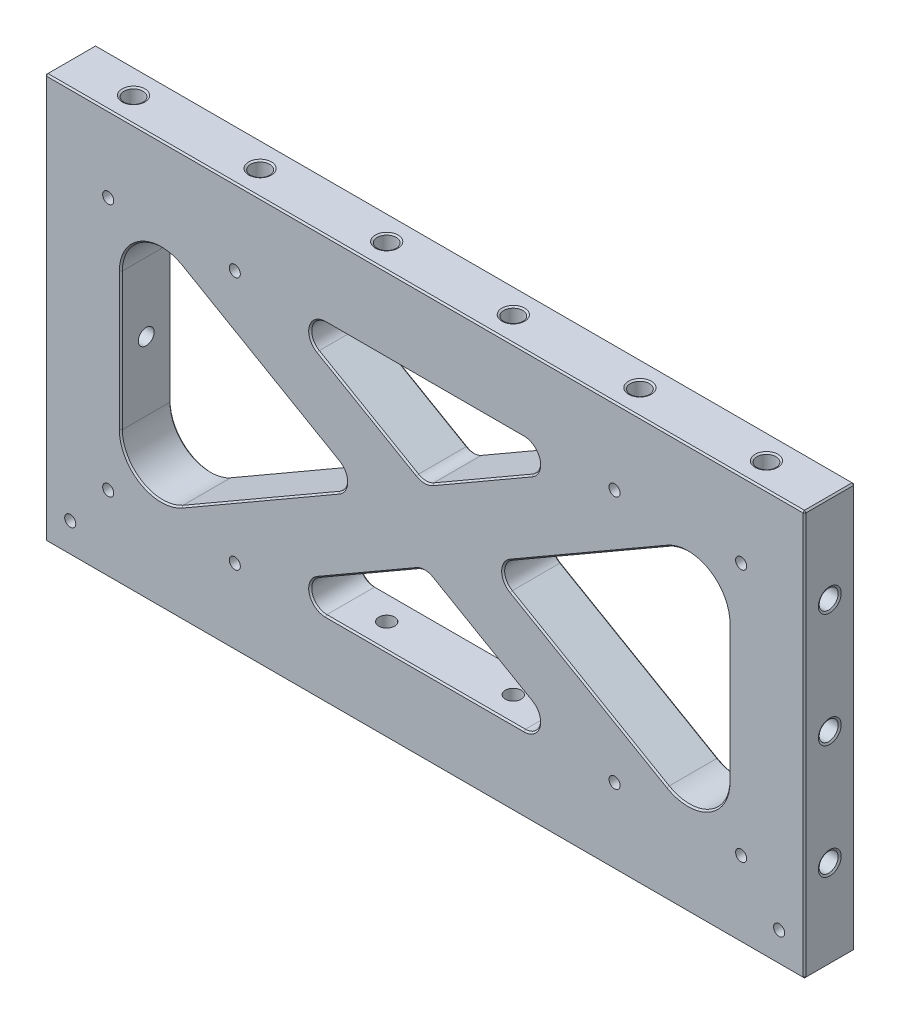
SolidWorks part; units mm, degrees
material "6061-T6 Al"
ref_plane "Front" through (0, 0, 0) normal (0, 0, 1) x (1, 0, 0)
ref_plane "Top" through (0, 0, 0) normal (0, 1, 0) x (1, 0, 0)
ref_plane "Right" through (0, 0, 0) normal (1, 0, 0) x (0, 0, -1)
sketch "Sketch1" plane through (0, 0, 0) normal (0, 0, 1) x (1, 0, 0)
  line L1 (-190.5, 0) -> (190.5, 0)
  line L2 (-190.5, 0) -> (-190.5, 203.2)
  line L3 (-190.5, 203.2) -> (190.5, 203.2)
  line L4 (190.5, 0) -> (190.5, 203.2)
  dimension "D1" = 203.2
  dimension "D2" = 381
extrude "Extrude1" add sketch "Sketch1" along normal mid plane 25.4
sketch "Sketch22" plane through (0, 0, 12.7) normal (0, 0, 1) x (1, 0, 0)
  line L0 (0, 0) -> (0, 38.1) construction
  line L1 (-152.4, 165.1) -> (152.4, 165.1)
  line L2 (-152.4, 165.1) -> (-152.4, 38.1)
  line L3 (-152.4, 38.1) -> (152.4, 38.1)
  line L4 (152.4, 165.1) -> (152.4, 38.1)
  line L5 (152.4, 101.6) -> (190.5, 101.6) construction
  line L6 (190.5, 0) -> (190.5, 203.2) construction
  line L7 (-190.5, 0) -> (190.5, 0) construction
  dimension "D1" = 38.1
  dimension "D2" = 38.1
extrude "Extrude2" cut sketch "Sketch22" against normal through all
sketch "Sketch23" plane through (0, 0, 12.7) normal (0, 0, 1) x (1, 0, 0)
  line L0 (-141.7352, 165.1) -> (78.2352, 38.1)
  line L1 (152.4, 165.1) -> (-152.4, 165.1) construction
  line L2 (-152.4, 38.1) -> (152.4, 38.1) construction
  line L3 (78.2352, 38.1) -> (141.7352, 38.1)
  line L4 (141.7352, 38.1) -> (-78.2352, 165.1)
  line L5 (-78.2352, 165.1) -> (-141.7352, 165.1)
  line L6 (-109.9852, 165.1) -> (109.9852, 38.1) construction
  point P10 (0, 101.6)
  dimension "D1" = 31.75
  dimension "D2" = 30
extrude "Extrude3" add sketch "Sketch23" against normal up to surface (25.4 mm away) up to face at (0, 101.6, -12.7)
mirror "Mirror2" about plane through (0, 0, 0) normal (1, 0, 0) of "Extrude3"
sketch "Sketch25" plane through (0, 0, -12.7) normal (0, 0, -1) x (-1, 0, 0)
  line L0 (-152.4, 136.062) -> (-152.4, 165.1)
  line L1 (-152.4, 38.1) -> (-152.4, 165.1) construction
  line L2 (-152.4, 165.1) -> (-141.7352, 165.1)
  line L3 (-141.7352, 165.1) -> (-121.92, 153.6597)
  line L4 (-141.7352, 165.1) -> (-31.75, 101.6) construction
  line L5 (0, 119.9309) -> (0, 165.1) construction
  line L6 (-78.2352, 165.1) -> (78.2352, 165.1) construction
  line L7 (141.7352, 165.1) -> (121.92, 153.6597)
  line L8 (152.4, 165.1) -> (141.7352, 165.1)
  line L9 (152.4, 136.062) -> (152.4, 165.1)
  line L10 (31.75, 101.6) -> (152.4, 101.6) construction
  line L11 (152.4, 165.1) -> (152.4, 38.1) construction
  line L12 (152.4, 67.138) -> (152.4, 38.1)
  line L13 (152.4, 38.1) -> (141.7352, 38.1)
  line L14 (141.7352, 38.1) -> (121.92, 49.5403)
  line L15 (-141.7352, 38.1) -> (-121.92, 49.5403)
  line L16 (-152.4, 38.1) -> (-141.7352, 38.1)
  line L17 (-152.4, 67.138) -> (-152.4, 38.1)
  arc A0 (-152.4, 136.062) -> (-121.92, 153.6597) centre (-132.08, 136.062) cw
  arc A1 (152.4, 136.062) -> (121.92, 153.6597) centre (132.08, 136.062) ccw
  arc A2 (152.4, 67.138) -> (121.92, 49.5403) centre (132.08, 67.138) cw
  arc A3 (-152.4, 67.138) -> (-121.92, 49.5403) centre (-132.08, 67.138) ccw
  dimension "D1" = 20.32
extrude "Extrude4" add sketch "Sketch25" against normal up to surface (25.4 mm away) up to face at (124.0041, 101.6, 12.7)
fillet "Fillet2" radius 7.62 8 edges at (-78.2352, 165.1, 0) (78.2352, 165.1, 0) (0, 119.9309, 0) (0, 83.2691, 0) (78.2352, 38.1, 0) (-78.2352, 38.1, 0) (-31.75, 101.6, 0) (31.75, 101.6, 0)
chamfer "Chamfer1" distance 0.762 angle 45 12 edges at (0, 0, 12.7) (190.5, 0, 0) (0, 0, -12.7) (-190.5, 101.6, 12.7) (-190.5, 0, 0) (-190.5, 101.6, -12.7) (190.5, 203.2, 0) (0, 203.2, 12.7) (-190.5, 203.2, 0) (0, 203.2, -12.7) (190.5, 101.6, 12.7) (190.5, 101.6, -12.7)
chamfer "Chamfer2" distance 0.762 angle 45 48 edges at (142.24, 153.6597, 12.7) (142.24, 153.6597, -12.7) (152.4, 101.6, 12.7) (82.55, 130.9294, 12.7) (82.55, 130.9294, -12.7) (142.24, 49.5403, 12.7) (142.24, 49.5403, -12.7) (39.37, 101.6, 12.7) (82.55, 72.2706, 12.7) (82.55, 72.2706, -12.7) (152.4, 101.6, -12.7) (39.37, 101.6, -12.7) (57.1574, 159.4522, 12.7) (28.7085, 136.5057, 12.7) (28.7085, 136.5057, -12.7) (0, 165.1, 12.7) (0, 121.1097, 12.7) (-57.1574, 159.4522, 12.7) (-28.7085, 136.5057, 12.7) (-28.7085, 136.5057, -12.7) (57.1574, 159.4522, -12.7) (0, 165.1, -12.7) (0, 121.1097, -12.7) (-57.1574, 159.4522, -12.7) (-82.55, 130.9294, -12.7) (-82.55, 130.9294, 12.7) (-142.24, 153.6597, 12.7) (-142.24, 153.6597, -12.7) (-39.37, 101.6, -12.7) (-152.4, 101.6, -12.7) (-82.55, 72.2706, 12.7) (-82.55, 72.2706, -12.7) (-142.24, 49.5403, 12.7) (-142.24, 49.5403, -12.7) (-39.37, 101.6, 12.7) (-152.4, 101.6, 12.7) (0, 82.0903, -12.7) (-28.7085, 66.6943, -12.7) (-28.7085, 66.6943, 12.7) (28.7085, 66.6943, 12.7) (28.7085, 66.6943, -12.7) (-57.1574, 43.7478, -12.7) (57.1574, 43.7478, -12.7) (0, 38.1, -12.7) (0, 82.0903, 12.7) (-57.1574, 43.7478, 12.7) (57.1574, 43.7478, 12.7) (0, 38.1, 12.7)
hole_wizard "3/8-16 Tapped Hole1" positions "Sketch7" profile "Sketch6" tap size "3/8-16" standard "Ansi Inch"
sketch "Sketch7" plane through (0, 0, 0) normal (0, -1, 0) x (1, 0, 0)
  line L8 (-158.75, 0) -> (-95.25, 0) construction
  line L9 (-95.25, 0) -> (-31.75, 0) construction
  line L10 (-31.75, 0) -> (31.75, 0) construction
  line L11 (31.75, 0) -> (95.25, 0) construction
  line L12 (95.25, 0) -> (158.75, 0) construction
  point P5 (-31.75, 0)
  point P7 (31.75, 0)
  dimension "D2" = 63.5
sketch "Sketch6" plane through (-31.75, 0, 0) normal (1, 0, 0) x (0, 0, -1)
  line L0 (0, 0) -> (0, 46.8347)
  line L1 (0, 46.8347) -> (3.9687, 44.45)
  line L2 (3.9687, 44.45) -> (3.9687, 25.4)
  line L3 (3.9687, 25.4) -> (4.7625, 25.4)
  line L5 (4.7625, 25.4) -> (4.7625, 0.5499)
  line L6 (4.7625, 0.5499) -> (5.715, 0)
  line L7 (5.715, 0) -> (0, 0)
  line L8 (-4.7625, 0.5499) -> (-5.715, 0) construction
  line L10 (0, 46.8347) -> (-3.9688, 44.45) construction
  line L11 (0, -6.35) -> (0, 107.95) construction
  dimension "Tap Drill Dia." = 7.9375
  dimension "Tap Drill Depth" = 44.45
  dimension "Thread Major Dia." = 9.525
  dimension "Thread Depth" = 25.4
  dimension "Near C'Sink Dia." = 11.43
  dimension "Near C'Sink Angle" = 120
  dimension "Drill Angle" = 118
hole_wizard "3/8-16 Tapped Hole2" positions "Sketch49" profile "Sketch48" tap size "3/8-16" standard "Ansi Inch"
sketch "Sketch49" plane through (0, 0, 0) normal (0, -1, 0) x (1, 0, 0)
  point P1 (-95.25, 0)
  point P4 (95.25, 0)
sketch "Sketch48" plane through (-95.25, 0, 0) normal (1, 0, 0) x (0, 0, -1)
  line L0 (0, 0) -> (0, 46.8347)
  line L1 (0, 46.8347) -> (3.9687, 44.45)
  line L2 (3.9687, 44.45) -> (3.9687, 25.4)
  line L3 (3.9687, 25.4) -> (4.7625, 25.4)
  line L5 (4.7625, 25.4) -> (4.7625, 0.5499)
  line L6 (4.7625, 0.5499) -> (5.715, 0)
  line L7 (5.715, 0) -> (0, 0)
  line L8 (-4.7625, 0.5499) -> (-5.715, 0) construction
  line L10 (0, 46.8347) -> (-3.9688, 44.45) construction
  line L11 (0, -6.35) -> (0, 107.95) construction
  dimension "Tap Drill Dia." = 7.9375
  dimension "Tap Drill Depth" = 44.45
  dimension "Thread Major Dia." = 9.525
  dimension "Thread Depth" = 25.4
  dimension "Near C'Sink Dia." = 11.43
  dimension "Near C'Sink Angle" = 120
  dimension "Drill Angle" = 118
hole_wizard "3/8-16 Tapped Hole9" positions "Sketch58" profile "Sketch57" tap size "3/8-16" standard "Ansi Inch"
sketch "Sketch58" plane through (0, 0, 0) normal (0, -1, 0) x (1, 0, 0)
  point P1 (158.75, 0)
  point P4 (-158.75, 0)
sketch "Sketch57" plane through (158.75, 0, 0) normal (1, 0, 0) x (0, 0, -1)
  line L0 (0, 0) -> (0, 46.8347)
  line L1 (0, 46.8347) -> (3.9687, 44.45)
  line L2 (3.9687, 44.45) -> (3.9687, 25.4)
  line L3 (3.9687, 25.4) -> (4.7625, 25.4)
  line L5 (4.7625, 25.4) -> (4.7625, 0.5499)
  line L6 (4.7625, 0.5499) -> (5.715, 0)
  line L7 (5.715, 0) -> (0, 0)
  line L8 (-4.7625, 0.5499) -> (-5.715, 0) construction
  line L10 (0, 46.8347) -> (-3.9688, 44.45) construction
  line L11 (0, -6.35) -> (0, 107.95) construction
  dimension "Tap Drill Dia." = 7.9375
  dimension "Tap Drill Depth" = 44.45
  dimension "Thread Major Dia." = 9.525
  dimension "Thread Depth" = 25.4
  dimension "Near C'Sink Dia." = 11.43
  dimension "Near C'Sink Angle" = 120
  dimension "Drill Angle" = 118
hole_wizard "3/8-16 Tapped Hole3" positions "Sketch9" profile "Sketch8" tap size "3/8-16" standard "Ansi Inch"
sketch "Sketch9" plane through (0, 203.2, 0) normal (0, 1, 0) x (-1, 0, 0)
  point P6 (31.75, 0)
  point P8 (-31.75, 0)
sketch "Sketch8" plane through (-31.75, 203.2, 0) normal (1, 0, 0) x (0, 0, 1)
  line L0 (0, 0) -> (0, 46.8347)
  line L1 (0, 46.8347) -> (3.9687, 44.45)
  line L2 (3.9687, 44.45) -> (3.9687, 25.4)
  line L3 (3.9687, 25.4) -> (4.7625, 25.4)
  line L5 (4.7625, 25.4) -> (4.7625, 0.5499)
  line L6 (4.7625, 0.5499) -> (5.715, 0)
  line L7 (5.715, 0) -> (0, 0)
  line L8 (-4.7625, 0.5499) -> (-5.715, 0) construction
  line L10 (0, 46.8347) -> (-3.9688, 44.45) construction
  line L11 (0, -6.35) -> (0, 107.95) construction
  dimension "Tap Drill Dia." = 7.9375
  dimension "Tap Drill Depth" = 44.45
  dimension "Thread Major Dia." = 9.525
  dimension "Thread Depth" = 25.4
  dimension "Near C'Sink Dia." = 11.43
  dimension "Near C'Sink Angle" = 120
  dimension "Drill Angle" = 118
hole_wizard "3/8-16 Tapped Hole4" positions "Sketch51" profile "Sketch50" tap size "3/8-16" standard "Ansi Inch"
sketch "Sketch51" plane through (0, 203.2, 0) normal (0, 1, 0) x (-1, 0, 0)
  point P1 (-95.25, 0)
  point P10 (95.25, 0)
sketch "Sketch50" plane through (95.25, 203.2, 0) normal (1, 0, 0) x (0, 0, 1)
  line L0 (0, 0) -> (0, 46.8347)
  line L1 (0, 46.8347) -> (3.9687, 44.45)
  line L2 (3.9687, 44.45) -> (3.9687, 25.4)
  line L3 (3.9687, 25.4) -> (4.7625, 25.4)
  line L5 (4.7625, 25.4) -> (4.7625, 0.5499)
  line L6 (4.7625, 0.5499) -> (5.715, 0)
  line L7 (5.715, 0) -> (0, 0)
  line L8 (-4.7625, 0.5499) -> (-5.715, 0) construction
  line L10 (0, 46.8347) -> (-3.9688, 44.45) construction
  line L11 (0, -6.35) -> (0, 107.95) construction
  dimension "Tap Drill Dia." = 7.9375
  dimension "Tap Drill Depth" = 44.45
  dimension "Thread Major Dia." = 9.525
  dimension "Thread Depth" = 25.4
  dimension "Near C'Sink Dia." = 11.43
  dimension "Near C'Sink Angle" = 120
  dimension "Drill Angle" = 118
hole_wizard "3/8-16 Tapped Hole10" positions "Sketch60" profile "Sketch59" tap size "3/8-16" standard "Ansi Inch"
sketch "Sketch60" plane through (0, 203.2, 0) normal (0, 1, 0) x (-1, 0, 0)
  point P1 (-158.75, 0)
  point P4 (158.75, 0)
sketch "Sketch59" plane through (158.75, 203.2, 0) normal (1, 0, 0) x (0, 0, 1)
  line L0 (0, 0) -> (0, 46.8347)
  line L1 (0, 46.8347) -> (3.9687, 44.45)
  line L2 (3.9687, 44.45) -> (3.9687, 25.4)
  line L3 (3.9687, 25.4) -> (4.7625, 25.4)
  line L5 (4.7625, 25.4) -> (4.7625, 0.5499)
  line L6 (4.7625, 0.5499) -> (5.715, 0)
  line L7 (5.715, 0) -> (0, 0)
  line L8 (-4.7625, 0.5499) -> (-5.715, 0) construction
  line L10 (0, 46.8347) -> (-3.9688, 44.45) construction
  line L11 (0, -6.35) -> (0, 107.95) construction
  dimension "Tap Drill Dia." = 7.9375
  dimension "Tap Drill Depth" = 44.45
  dimension "Thread Major Dia." = 9.525
  dimension "Thread Depth" = 25.4
  dimension "Near C'Sink Dia." = 11.43
  dimension "Near C'Sink Angle" = 120
  dimension "Drill Angle" = 118
hole_wizard "7/32 (0.21875) Vent Hole1" positions "Sketch5" profile "Sketch4" hole size "7/32" standard "Ansi Inch" end condition through all
sketch "Sketch5" plane through (-328.9333, 96.8735, 12.7) normal (0, 0, -1) x (-1, 0, 0)
  line L24 (-518.6713, -96.8735) -> (-139.1953, -96.8735) construction
  line L25 (-139.1953, 106.3265) -> (-518.6713, 106.3265) construction
  point P149 (-487.6833, -58.7735)
  point P151 (-424.1833, -58.7735)
  point P153 (-233.6833, -58.7735)
  point P155 (-170.1833, -58.7735)
  point P157 (-487.6833, 68.2265)
  point P159 (-424.1833, 68.2265)
  point P161 (-233.6833, 68.2265)
  point P163 (-170.1833, 68.2265)
  dimension "D1" = 38.1
  dimension "D2" = 38.1
sketch "Sketch4" plane through (158.75, 38.1, 12.7) normal (1, 0, 0) x (0, -1, 0)
  line L0 (0, 0) -> (0, 25.4)
  line L1 (0, 25.4) -> (2.7781, 25.4)
  line L2 (2.7781, 25.4) -> (2.7781, 0)
  line L5 (2.7781, 0) -> (0, 0)
  line L11 (0, -6.35) -> (0, 107.95) construction
  dimension "Thru Hole Dia." = 5.5562
  dimension "Thru Hole Depth" = 25.4
hole_wizard "3/8-16 Tapped Hole5" positions "Sketch19" profile "Sketch18" tap size "3/8-16" standard "Ansi Inch"
sketch "Sketch19" plane through (190.5, 0, 0) normal (1, 0, 0) x (0, 0, -1)
  line L1 (0, 158.75) -> (0, 101.6) construction
  line L2 (0, 101.6) -> (0, 44.45) construction
  line L10 (0, 101.6) -> (12.7, 101.6) construction
  line L11 (12.7, 0) -> (12.7, 203.2) construction
  point P5 (0, 101.6)
  dimension "D1" = 57.15
sketch "Sketch18" plane through (190.5, 101.6, 0) normal (0, 1, 0) x (0, 0, -1)
  line L0 (0, 0) -> (0, 40.4847)
  line L1 (0, 40.4847) -> (3.9687, 38.1)
  line L2 (3.9687, 38.1) -> (3.9687, 25.4)
  line L3 (3.9687, 25.4) -> (4.7625, 25.4)
  line L5 (4.7625, 25.4) -> (4.7625, 0.5499)
  line L6 (4.7625, 0.5499) -> (5.715, 0)
  line L7 (5.715, 0) -> (0, 0)
  line L8 (-4.7625, 0.5499) -> (-5.715, 0) construction
  line L10 (0, 40.4847) -> (-3.9688, 38.1) construction
  line L11 (0, -6.35) -> (0, 107.95) construction
  dimension "Tap Drill Dia." = 7.9375
  dimension "Tap Drill Depth" = 38.1
  dimension "Thread Major Dia." = 9.525
  dimension "Thread Depth" = 25.4
  dimension "Near C'Sink Dia." = 11.43
  dimension "Near C'Sink Angle" = 120
  dimension "Drill Angle" = 118
hole_wizard "3/8-16 Tapped Hole6" positions "Sketch53" profile "Sketch52" tap size "3/8-16" standard "Ansi Inch"
sketch "Sketch53" plane through (190.5, 0, 0) normal (1, 0, 0) x (0, 0, -1)
  point P0 (0, 158.75)
  point P4 (0, 44.45)
sketch "Sketch52" plane through (190.5, 158.75, 0) normal (0, 1, 0) x (0, 0, -1)
  line L0 (0, 0) -> (0, 35.4047)
  line L1 (0, 35.4047) -> (3.9687, 33.02)
  line L2 (3.9687, 33.02) -> (3.9687, 25.4)
  line L3 (3.9687, 25.4) -> (4.7625, 25.4)
  line L5 (4.7625, 25.4) -> (4.7625, 0.5499)
  line L6 (4.7625, 0.5499) -> (5.715, 0)
  line L7 (5.715, 0) -> (0, 0)
  line L8 (-4.7625, 0.5499) -> (-5.715, 0) construction
  line L10 (0, 35.4047) -> (-3.9688, 33.02) construction
  line L11 (0, -6.35) -> (0, 107.95) construction
  dimension "Tap Drill Dia." = 7.9375
  dimension "Tap Drill Depth" = 33.02
  dimension "Thread Major Dia." = 9.525
  dimension "Thread Depth" = 25.4
  dimension "Near C'Sink Dia." = 11.43
  dimension "Near C'Sink Angle" = 120
  dimension "Drill Angle" = 118
hole_wizard "3/8-16 Tapped Hole7" positions "Sketch21" profile "Sketch20" tap size "3/8-16" standard "Ansi Inch"
sketch "Sketch21" plane through (-190.5, 0, 0) normal (-1, 0, 0) x (0, 0, 1)
  point P1 (0, 101.6)
sketch "Sketch20" plane through (-190.5, 101.6, 0) normal (0, 1, 0) x (0, 0, 1)
  line L0 (0, 0) -> (0, 40.4847)
  line L1 (0, 40.4847) -> (3.9687, 38.1)
  line L2 (3.9687, 38.1) -> (3.9687, 25.4)
  line L3 (3.9687, 25.4) -> (4.7625, 25.4)
  line L5 (4.7625, 25.4) -> (4.7625, 0.5499)
  line L6 (4.7625, 0.5499) -> (5.715, 0)
  line L7 (5.715, 0) -> (0, 0)
  line L8 (-4.7625, 0.5499) -> (-5.715, 0) construction
  line L10 (0, 40.4847) -> (-3.9688, 38.1) construction
  line L11 (0, -6.35) -> (0, 107.95) construction
  dimension "Tap Drill Dia." = 7.9375
  dimension "Tap Drill Depth" = 38.1
  dimension "Thread Major Dia." = 9.525
  dimension "Thread Depth" = 25.4
  dimension "Near C'Sink Dia." = 11.43
  dimension "Near C'Sink Angle" = 120
  dimension "Drill Angle" = 118
hole_wizard "3/8-16 Tapped Hole8" positions "Sketch56" profile "Sketch55" tap size "3/8-16" standard "Ansi Inch"
sketch "Sketch56" plane through (-190.5, 0, 0) normal (-1, 0, 0) x (0, 0, 1)
  point P1 (0, 158.75)
  point P4 (0, 44.45)
sketch "Sketch55" plane through (-190.5, 158.75, 0) normal (0, 1, 0) x (0, 0, 1)
  line L0 (0, 0) -> (0, 35.4047)
  line L1 (0, 35.4047) -> (3.9687, 33.02)
  line L2 (3.9687, 33.02) -> (3.9687, 25.4)
  line L3 (3.9687, 25.4) -> (4.7625, 25.4)
  line L5 (4.7625, 25.4) -> (4.7625, 0.5499)
  line L6 (4.7625, 0.5499) -> (5.715, 0)
  line L7 (5.715, 0) -> (0, 0)
  line L8 (-4.7625, 0.5499) -> (-5.715, 0) construction
  line L10 (0, 35.4047) -> (-3.9688, 33.02) construction
  line L11 (0, -6.35) -> (0, 107.95) construction
  dimension "Tap Drill Dia." = 7.9375
  dimension "Tap Drill Depth" = 33.02
  dimension "Thread Major Dia." = 9.525
  dimension "Thread Depth" = 25.4
  dimension "Near C'Sink Dia." = 11.43
  dimension "Near C'Sink Angle" = 120
  dimension "Drill Angle" = 118
sketch "Sketch26" [suppressed] plane through (0, 0, 0) normal (0, -1, 0) x (1, 0, 0)
  line L4 (-190.5, -12.7) -> (190.5, -12.7)
  line L5 (190.5, -12.7) -> (190.5, 12.7)
  line L6 (190.5, 12.7) -> (-190.5, 12.7)
  line L7 (-190.5, 12.7) -> (-190.5, -12.7)
  line L8 (-190.5, -12.7) -> (190.5, -12.7)
  line L9 (190.5, -12.7) -> (190.5, 12.7)
  line L10 (190.5, 12.7) -> (-190.5, 12.7)
  line L11 (-190.5, 12.7) -> (-190.5, -12.7)
  dimension "D1" = 0
extrude "Extrude5" [suppressed] cut sketch "Sketch26" against normal blind 0.0254
sketch "Sketch27" [suppressed] plane through (0, 203.2, 0) normal (0, 1, 0) x (1, 0, 0)
  line L4 (190.5, 12.7) -> (-190.5, 12.7)
  line L5 (-190.5, 12.7) -> (-190.5, -12.7)
  line L6 (-190.5, -12.7) -> (190.5, -12.7)
  line L7 (190.5, -12.7) -> (190.5, 12.7)
  line L8 (190.5, 12.7) -> (-190.5, 12.7)
  line L9 (-190.5, 12.7) -> (-190.5, -12.7)
  line L10 (-190.5, -12.7) -> (190.5, -12.7)
  line L11 (190.5, -12.7) -> (190.5, 12.7)
  dimension "D1" = 0
extrude "Extrude6" [suppressed] cut sketch "Sketch27" against normal blind 0.0254
sketch "Sketch28" [suppressed] plane through (-190.5, 0, 0) normal (-1, 0, 0) x (0, 0, 1)
  line L4 (12.7, 203.1746) -> (-12.7, 203.1746)
  line L5 (-12.7, 203.1746) -> (-12.7, 0.0254)
  line L6 (-12.7, 0.0254) -> (12.7, 0.0254)
  line L7 (12.7, 0.0254) -> (12.7, 203.1746)
  line L8 (12.7, 203.1746) -> (-12.7, 203.1746)
  line L9 (-12.7, 203.1746) -> (-12.7, 0.0254)
  line L10 (-12.7, 0.0254) -> (12.7, 0.0254)
  line L11 (12.7, 0.0254) -> (12.7, 203.1746)
  dimension "D1" = 0
extrude "Extrude7" [suppressed] cut sketch "Sketch28" against normal blind 0.0254
sketch "Sketch29" [suppressed] plane through (190.5, 0, 0) normal (1, 0, 0) x (0, 0, -1)
  line L4 (12.7, 203.1746) -> (-12.7, 203.1746)
  line L5 (-12.7, 203.1746) -> (-12.7, 0.0254)
  line L6 (-12.7, 0.0254) -> (12.7, 0.0254)
  line L7 (12.7, 0.0254) -> (12.7, 203.1746)
  line L8 (12.7, 203.1746) -> (-12.7, 203.1746)
  line L9 (-12.7, 203.1746) -> (-12.7, 0.0254)
  line L10 (-12.7, 0.0254) -> (12.7, 0.0254)
  line L11 (12.7, 0.0254) -> (12.7, 203.1746)
  dimension "D1" = 0
extrude "Extrude8" [suppressed] cut sketch "Sketch29" against normal blind 0.0254
sketch "Sketch30" [suppressed] plane through (0, 0.0254, 0) normal (0, -1, 0) x (1, 0, 0)
  line L0 (190.4746, 12.7) -> (-190.4746, 12.7) construction
  line L1 (-19.05, 12.7) -> (-44.45, 12.7)
  line L2 (-19.05, 12.7) -> (-19.05, -12.7)
  line L3 (-19.05, -12.7) -> (-44.45, -12.7)
  line L4 (-44.45, 12.7) -> (-44.45, -12.7)
  line L5 (-190.4746, -12.7) -> (190.4746, -12.7) construction
  line L6 (107.95, 0) -> (146.05, 0) construction
  line L7 (-82.55, 12.7) -> (-107.95, 12.7)
  line L8 (-82.55, 12.7) -> (-82.55, -12.7)
  line L9 (-82.55, -12.7) -> (-107.95, -12.7)
  line L10 (-107.95, 12.7) -> (-107.95, -12.7)
  line L11 (-146.05, 12.7) -> (-171.45, 12.7)
  line L12 (-146.05, 12.7) -> (-146.05, -12.7)
  line L13 (-146.05, -12.7) -> (-171.45, -12.7)
  line L14 (-171.45, 12.7) -> (-171.45, -12.7)
  line L15 (19.05, 12.7) -> (44.45, 12.7)
  line L16 (19.05, 12.7) -> (19.05, -12.7)
  line L17 (19.05, -12.7) -> (44.45, -12.7)
  line L18 (44.45, 12.7) -> (44.45, -12.7)
  line L19 (82.55, 12.7) -> (107.95, 12.7)
  line L20 (82.55, 12.7) -> (82.55, -12.7)
  line L21 (82.55, -12.7) -> (107.95, -12.7)
  line L22 (107.95, 12.7) -> (107.95, -12.7)
  line L23 (146.05, 12.7) -> (171.45, 12.7)
  line L24 (146.05, 12.7) -> (146.05, -12.7)
  line L25 (146.05, -12.7) -> (171.45, -12.7)
  line L26 (171.45, 12.7) -> (171.45, -12.7)
  line L27 (44.45, 0) -> (82.55, 0) construction
  line L28 (-19.05, 0) -> (19.05, 0) construction
  line L29 (-82.55, 0) -> (-44.45, 0) construction
  line L30 (-146.05, 0) -> (-107.95, 0) construction
  dimension "D1" = 25.4
  dimension "D2" = 38.1
extrude "Extrude9" [suppressed] add sketch "Sketch30" along normal blind 0.0254
sketch "Sketch31" [suppressed] plane through (0, 203.1746, 0) normal (0, 1, 0) x (1, 0, 0)
  line L0 (190.4746, 12.7) -> (-190.4746, 12.7) construction
  line L1 (-171.45, 12.7) -> (-146.05, 12.7)
  line L2 (-171.45, 12.7) -> (-171.45, -12.7)
  line L3 (-171.45, -12.7) -> (-146.05, -12.7)
  line L4 (-146.05, 12.7) -> (-146.05, -12.7)
  line L5 (-190.4746, -12.7) -> (190.4746, -12.7) construction
  line L6 (-146.05, 0) -> (-107.95, 0) construction
  line L7 (-107.95, 12.7) -> (-82.55, 12.7)
  line L8 (-107.95, 12.7) -> (-107.95, -12.7)
  line L9 (-107.95, -12.7) -> (-82.55, -12.7)
  line L10 (-82.55, 12.7) -> (-82.55, -12.7)
  line L11 (-44.45, 12.7) -> (-19.05, 12.7)
  line L12 (-44.45, 12.7) -> (-44.45, -12.7)
  line L13 (-44.45, -12.7) -> (-19.05, -12.7)
  line L14 (-19.05, 12.7) -> (-19.05, -12.7)
  line L15 (19.05, 12.7) -> (44.45, 12.7)
  line L16 (19.05, 12.7) -> (19.05, -12.7)
  line L17 (19.05, -12.7) -> (44.45, -12.7)
  line L18 (44.45, 12.7) -> (44.45, -12.7)
  line L19 (82.55, 12.7) -> (107.95, 12.7)
  line L20 (82.55, 12.7) -> (82.55, -12.7)
  line L21 (82.55, -12.7) -> (107.95, -12.7)
  line L22 (107.95, 12.7) -> (107.95, -12.7)
  line L23 (146.05, 12.7) -> (171.45, 12.7)
  line L24 (146.05, 12.7) -> (146.05, -12.7)
  line L25 (146.05, -12.7) -> (171.45, -12.7)
  line L26 (171.45, 12.7) -> (171.45, -12.7)
  line L27 (-82.55, 0) -> (-44.45, 0) construction
  line L28 (-19.05, 0) -> (19.05, 0) construction
  line L29 (44.45, 0) -> (82.55, 0) construction
  line L30 (107.95, 0) -> (146.05, 0) construction
  dimension "D1" = 38.1
  dimension "D2" = 25.4
extrude "Extrude10" [suppressed] add sketch "Sketch31" along normal blind 0.0254
sketch "Sketch32" [suppressed] plane through (190.4746, 0, 0) normal (1, 0, 0) x (0, 0, -1)
  line L0 (-12.7, 203.1746) -> (-12.7, 0.0254) construction
  line L1 (-12.7, 57.15) -> (12.7, 57.15)
  line L2 (-12.7, 57.15) -> (-12.7, 31.75)
  line L3 (-12.7, 31.75) -> (12.7, 31.75)
  line L4 (12.7, 57.15) -> (12.7, 31.75)
  line L5 (12.7, 0.0254) -> (12.7, 203.1746) construction
  line L6 (0, 146.05) -> (0, 114.3) construction
  line L7 (-12.7, 114.3) -> (12.7, 114.3)
  line L8 (-12.7, 114.3) -> (-12.7, 88.9)
  line L9 (-12.7, 88.9) -> (12.7, 88.9)
  line L10 (12.7, 114.3) -> (12.7, 88.9)
  line L11 (-12.7, 171.45) -> (12.7, 171.45)
  line L12 (-12.7, 171.45) -> (-12.7, 146.05)
  line L13 (-12.7, 146.05) -> (12.7, 146.05)
  line L14 (12.7, 171.45) -> (12.7, 146.05)
  line L15 (0, 88.9) -> (0, 57.15) construction
  point P22 (12.7, 101.6)
  dimension "D1" = 25.4
  dimension "D2" = 31.75
extrude "Extrude11" [suppressed] add sketch "Sketch32" along normal blind 0.0254
sketch "Sketch33" [suppressed] plane through (-190.4746, 0, 0) normal (-1, 0, 0) x (0, 0, 1)
  line L0 (-12.7, 203.1746) -> (-12.7, 0.0254) construction
  line L1 (-12.7, 171.45) -> (12.7, 171.45)
  line L2 (-12.7, 171.45) -> (-12.7, 146.05)
  line L3 (-12.7, 146.05) -> (12.7, 146.05)
  line L4 (12.7, 171.45) -> (12.7, 146.05)
  line L5 (12.7, 0.0254) -> (12.7, 203.1746) construction
  line L6 (0, 146.05) -> (0, 114.3) construction
  line L7 (-12.7, 114.3) -> (12.7, 114.3)
  line L8 (-12.7, 114.3) -> (-12.7, 88.9)
  line L9 (-12.7, 88.9) -> (12.7, 88.9)
  line L10 (12.7, 114.3) -> (12.7, 88.9)
  line L11 (-12.7, 57.15) -> (12.7, 57.15)
  line L12 (-12.7, 57.15) -> (-12.7, 31.75)
  line L13 (-12.7, 31.75) -> (12.7, 31.75)
  line L14 (12.7, 57.15) -> (12.7, 31.75)
  line L15 (0, 88.9) -> (0, 57.15) construction
  point P20 (12.7, 101.6)
  dimension "D1" = 25.4
  dimension "D2" = 31.75
extrude "Extrude12" [suppressed] add sketch "Sketch33" along normal blind 0.0254
sketch "Sketch34" [suppressed] plane through (0, 0, 12.7) normal (0, 0, 1) x (1, 0, 0)
  line L0 (-152.4, 160.0482) -> (-152.4, 43.1518)
  line L1 (-152.4, 43.1518) -> (-126.6353, 43.1518)
  line L2 (-126.6353, 43.1518) -> (-25.4, 101.6)
  line L3 (-25.4, 101.6) -> (-126.6353, 160.0482)
  line L4 (-126.6353, 160.0482) -> (-152.4, 160.0482)
  line L5 (-152.4, 139.7282) -> (-152.4, 63.4718) construction
  line L6 (-121.92, 157.3258) -> (-36.83, 108.1991) construction
  line L7 (-121.92, 45.8742) -> (-36.83, 95.0009) construction
  arc A0 (-152.4, 63.4718) -> (-121.92, 45.8742) centre (-132.08, 63.4718) ccw construction
  arc A1 (-121.92, 157.3258) -> (-152.4, 139.7282) centre (-132.08, 139.7282) ccw construction
extrude "Extrude13" [suppressed] cut sketch "Sketch34" against normal through all
mirror "Mirror3" [suppressed] about plane through (0, 0, 0) normal (1, 0, 0)
sketch "Sketch35" [suppressed] plane through (0, 0, 12.7) normal (0, 0, 1) x (1, 0, 0)
  line L0 (-63.767, 165.1) -> (-63.767, 153.0806)
  line L1 (0, 116.2647) -> (63.767, 153.0806)
  line L2 (63.767, 165.1) -> (-63.767, 165.1)
  line L3 (56.147, 165.1) -> (-56.147, 165.1) construction
  line L6 (-63.767, 153.0806) -> (0, 116.2647)
  line L7 (63.767, 153.0806) -> (63.767, 165.1)
  line L8 (-3.81, 118.4644) -> (-59.957, 150.8809) construction
  line L9 (3.81, 118.4644) -> (59.957, 150.8809) construction
  line L10 (25.4, 101.6) -> (91.8669, 101.6) construction
  line L11 (63.767, 50.1194) -> (63.767, 38.1)
  line L12 (-63.767, 50.1194) -> (0, 86.9353)
  line L13 (63.767, 38.1) -> (-63.767, 38.1)
  line L14 (0, 86.9353) -> (63.767, 50.1194)
  line L15 (-63.767, 38.1) -> (-63.767, 50.1194)
  arc A0 (59.957, 150.8809) -> (56.147, 165.1) centre (56.147, 157.48) ccw construction
  arc A1 (-56.147, 165.1) -> (-59.957, 150.8809) centre (-56.147, 157.48) ccw construction
extrude "Extrude14" [suppressed] cut sketch "Sketch35" against normal through all
sketch "Sketch36" [suppressed] plane through (0, 203.2, 0) normal (0, 1, 0) x (1, 0, 0)
  line L0 (171.45, -12.7) -> (171.45, 12.7) construction
  line L1 (-171.45, 12.7) -> (171.45, 12.7)
  line L2 (-171.45, 12.7) -> (-171.45, 8.89)
  line L3 (-171.45, 8.89) -> (171.45, 8.89)
  line L4 (171.45, 12.7) -> (171.45, 8.89)
  line L5 (-171.45, 12.7) -> (-171.45, -12.7) construction
  line L6 (171.45, -12.7) -> (-171.45, -12.7)
  line L7 (171.45, -12.7) -> (171.45, -8.89)
  line L8 (171.45, -8.89) -> (-171.45, -8.89)
  line L9 (-171.45, -12.7) -> (-171.45, -8.89)
  dimension "D1" = 3.81
extrude "Extrude15" [suppressed] cut sketch "Sketch36" against normal up to surface (0.0254 mm away)
sketch "Sketch37" [suppressed] plane through (0, 0, 0) normal (0, -1, 0) x (1, 0, 0)
  line L0 (171.45, -12.7) -> (171.45, 12.7) construction
  line L1 (-171.45, 12.7) -> (171.45, 12.7)
  line L2 (-171.45, 12.7) -> (-171.45, 8.89)
  line L3 (-171.45, 8.89) -> (171.45, 8.89)
  line L4 (171.45, 12.7) -> (171.45, 8.89)
  line L6 (-171.45, -12.7) -> (171.45, -12.7)
  line L7 (-171.45, -12.7) -> (-171.45, -8.89)
  line L8 (-171.45, -8.89) -> (171.45, -8.89)
  line L9 (171.45, -12.7) -> (171.45, -8.89)
  dimension "D1" = 3.81
extrude "Extrude16" [suppressed] cut sketch "Sketch37" against normal up to surface (0.0254 mm away)
sketch "Sketch38" [suppressed] plane through (-190.5, 0, 0) normal (-1, 0, 0) x (0, 0, 1)
  line L0 (-12.7, 31.75) -> (12.7, 31.75) construction
  line L1 (-12.7, 171.45) -> (-8.89, 171.45)
  line L2 (-12.7, 171.45) -> (-12.7, 31.75)
  line L3 (-12.7, 31.75) -> (-8.89, 31.75)
  line L4 (-8.89, 171.45) -> (-8.89, 31.75)
  line L5 (12.7, 171.45) -> (-12.7, 171.45) construction
  line L6 (12.7, 31.75) -> (8.89, 31.75)
  line L7 (12.7, 31.75) -> (12.7, 171.45)
  line L8 (12.7, 171.45) -> (8.89, 171.45)
  line L9 (8.89, 31.75) -> (8.89, 171.45)
  dimension "D1" = 3.81
extrude "Extrude17" [suppressed] cut sketch "Sketch38" against normal up to surface (0.0254 mm away)
sketch "Sketch39" [suppressed] plane through (190.5, 0, 0) normal (1, 0, 0) x (0, 0, -1)
  line L0 (-12.7, 31.75) -> (12.7, 31.75) construction
  line L1 (-12.7, 171.45) -> (-8.89, 171.45)
  line L2 (-12.7, 171.45) -> (-12.7, 31.75)
  line L3 (-12.7, 31.75) -> (-8.89, 31.75)
  line L4 (-8.89, 171.45) -> (-8.89, 31.75)
  line L5 (12.7, 171.45) -> (-12.7, 171.45) construction
  line L6 (12.7, 31.75) -> (8.89, 31.75)
  line L7 (12.7, 31.75) -> (12.7, 171.45)
  line L8 (12.7, 171.45) -> (8.89, 171.45)
  line L9 (8.89, 31.75) -> (8.89, 171.45)
  dimension "D1" = 3.81
extrude "Extrude18" [suppressed] cut sketch "Sketch39" against normal up to surface (0.0254 mm away)
sketch "Sketch45" plane through (0, 0, 0) normal (0, -1, 0) x (1, 0, 0)
  line L0 (-179.3875, 0) -> (-176.2125, 0) construction
  line L1 (-179.3875, 4.7714) -> (-176.2125, 4.7714)
  line L2 (-179.3875, -4.7714) -> (-176.2125, -4.7714)
  line L4 (-190.5, -11.938) -> (-190.5, 11.938) construction
  line L5 (0, 0) -> (0, 105.6245) construction
  line L6 (179.3875, 0) -> (176.2125, 0) construction
  line L7 (179.3875, 4.7714) -> (176.2125, 4.7714)
  line L8 (179.3875, -4.7714) -> (176.2125, -4.7714)
  arc A0 (-179.3875, 4.7714) -> (-179.3875, -4.7714) centre (-179.3875, 0) ccw
  arc A1 (-176.2125, -4.7714) -> (-176.2125, 4.7714) centre (-176.2125, 0) ccw
  arc A2 (179.3875, 4.7714) -> (179.3875, -4.7714) centre (179.3875, 0) cw
  arc A3 (176.2125, -4.7714) -> (176.2125, 4.7714) centre (176.2125, 0) cw
  point P2 (-177.8, 0)
  point P17 (177.8, 0)
  dimension "D1" = 9.5428
  dimension "D2" = 3.175
  dimension "D3" = 12.7
extrude "Extrude20" cut sketch "Sketch45" against normal blind 19.05
chamfer "Chamfer4" distance 2.286 angle 45 8 edges at (-184.1589, 0, 0) (-177.8, 0, -4.7714) (-177.8, 0, 4.7714) (-171.4411, 0, 0) (171.4411, 0, 0) (177.8, 0, -4.7714) (177.8, 0, 4.7714) (184.1589, 0, 0)
hole_wizard "7/32 (0.21875) Diameter Hole3" positions "Sketch47" profile "Sketch46" hole size "7/32" standard "Ansi Inch" end condition through all
sketch "Sketch47" plane through (0, 0, 12.7) normal (0, 0, 1) x (1, 0, 0)
  line L2 (-177.8, 15.24) -> (-190.5, 15.24) construction
  line L3 (-190.5, 0.762) -> (-190.5, 202.438) construction
  line L6 (177.8, 15.24) -> (190.5, 15.24) construction
  line L7 (190.5, 202.438) -> (190.5, 0.762) construction
  line L10 (189.738, 0) -> (-189.738, 0) construction
  point P0 (177.8, 15.24)
  point P9 (-177.8, 15.24)
  dimension "D1" = 12.7
  dimension "D2" = 15.24
sketch "Sketch46" plane through (177.8, 15.24, 12.7) normal (1, 0, 0) x (0, -1, 0)
  line L0 (0, 0) -> (0, 25.4)
  line L1 (0, 25.4) -> (2.7781, 25.4)
  line L2 (2.7781, 25.4) -> (2.7781, 0)
  line L5 (2.7781, 0) -> (0, 0)
  line L11 (0, -6.35) -> (0, 107.95) construction
  dimension "Thru Hole Dia." = 5.5562
  dimension "Thru Hole Depth" = 25.4
